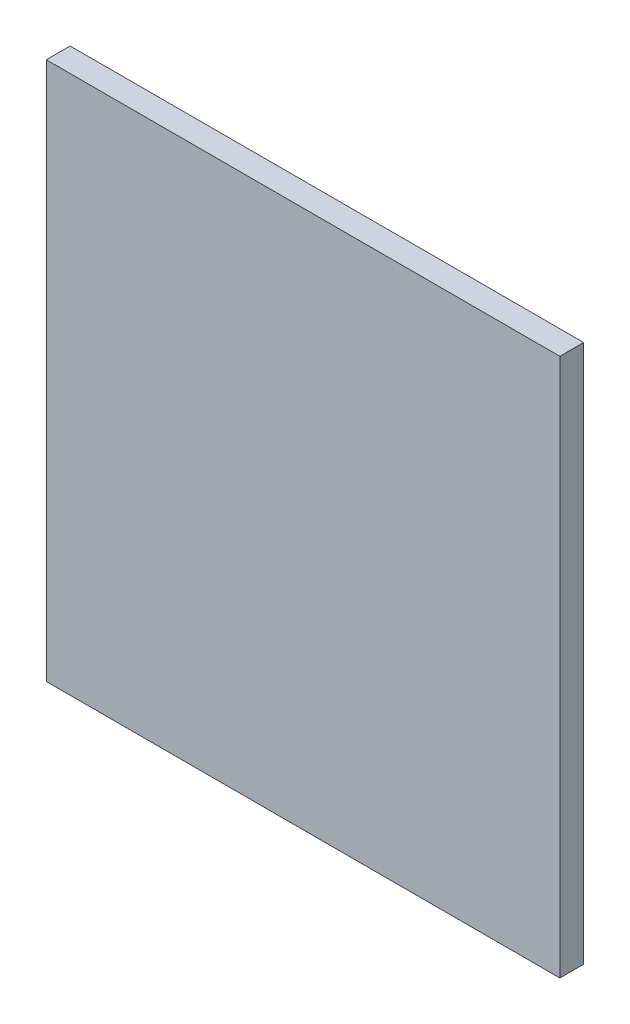
SolidWorks part; units mm, degrees
material "ABS PC"
ref_plane "Front Plane" through (0, 0, 0) normal (0, 0, 1) x (1, 0, 0)
ref_plane "Top Plane" through (0, 0, 0) normal (0, 1, 0) x (1, 0, 0)
ref_plane "Right Plane" through (0, 0, 0) normal (1, 0, 0) x (0, 0, -1)
sketch "Sketch1" plane through (0, 0, 0) normal (0, 0, 1) x (1, 0, 0)
  line L4 (-65.4525, -92.9166) -> (-65.4525, -75.7079)
  line L5 (-65.4525, -75.7079) -> (-81.8675, -75.7079)
  line L6 (-81.8675, -75.7079) -> (-81.8675, -92.9166)
  line L7 (-81.8675, -92.9166) -> (-65.4525, -92.9166)
  line L8 (-65.4525, -92.9166) -> (-65.4525, -75.7079)
  line L9 (-65.4525, -75.7079) -> (-81.8675, -75.7079)
  line L10 (-81.8675, -75.7079) -> (-81.8675, -92.9166)
  line L11 (-81.8675, -92.9166) -> (-65.4525, -92.9166)
  dimension "D1" = 0
extrude "Boss-Extrude1" add sketch "Sketch1" along normal blind 0.762
